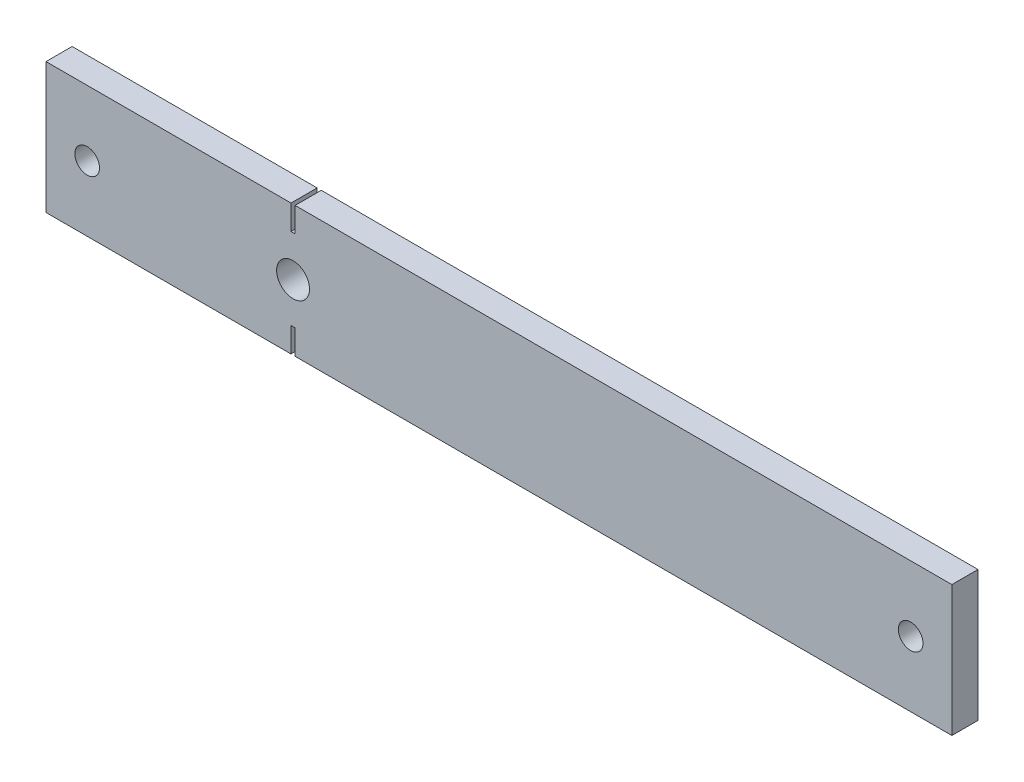
SolidWorks part; units mm, degrees
material "6060-T5"
ref_plane "Front Plane" through (0, 0, 0) normal (0, 0, 1) x (1, 0, 0)
ref_plane "Top Plane" through (0, 0, 0) normal (0, 1, 0) x (1, 0, 0)
ref_plane "Right Plane" through (0, 0, 0) normal (1, 0, 0) x (0, 0, -1)
sketch "Sketch1" plane through (0, 0, 0) normal (0, 0, 1) x (1, 0, 0)
  line L0 (60.5, 31.75) -> (220, 31.75)
  line L1 (0, 0) -> (59.5, 0)
  line L2 (0, 0) -> (0, 31.75)
  line L3 (0, 31.75) -> (59.5, 31.75)
  line L4 (220, 0) -> (220, 31.75)
  line L6 (59.5, 0) -> (59.5, 6)
  line L7 (59.5, 6) -> (60.5, 6)
  line L8 (60.5, 0) -> (60.5, 6)
  line L10 (59.5, 31.75) -> (59.5, 25.75)
  line L11 (59.5, 25.75) -> (60.5, 25.75)
  line L12 (60.5, 31.75) -> (60.5, 25.75)
  line L13 (60.5, 0) -> (220, 0)
  circle A0 centre (10, 15.875) radius 3
  circle A1 centre (60, 15.875) radius 4
  circle A2 centre (210, 15.875) radius 3
  dimension "D3" = 6
  dimension "D4" = 8
  dimension "D5" = 15.875
  dimension "D6" = 10
  dimension "D8" = 10
  dimension "D1" = 220
  dimension "D2" = 31.75
  dimension "D7" = 60
  dimension "D9" = 1
  dimension "D10" = 1
  dimension "D11" = 6
  dimension "D12" = 6
  dimension "D13" = 0.5
  dimension "D14" = 0.5
extrude "Boss-Extrude1" add sketch "Sketch1" along normal blind 6.35
